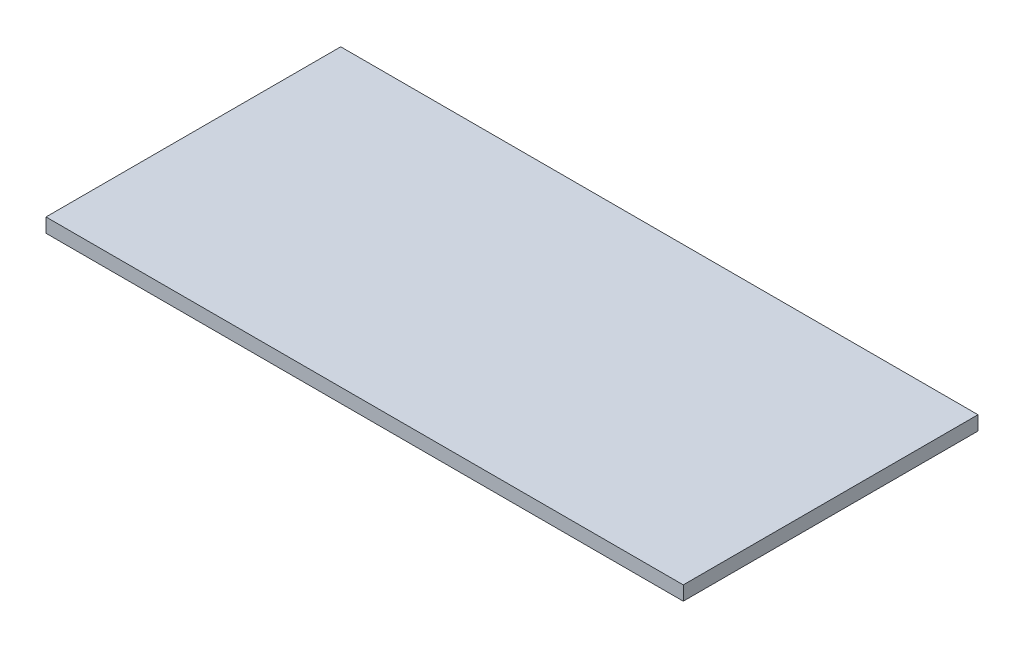
SolidWorks part; units mm, degrees
material "Plywood"
ref_plane "Front Plane" through (0, 0, 0) normal (0, 0, 1) x (1, 0, 0)
ref_plane "Top Plane" through (0, 0, 0) normal (0, 1, 0) x (1, 0, 0)
ref_plane "Right Plane" through (0, 0, 0) normal (1, 0, 0) x (0, 0, -1)
sketch "Sketch2" plane through (0, 0, 0) normal (0, 1, 0) x (1, 0, 0)
  line L1 (0, 0) -> (1143, 0)
  line L2 (0, 0) -> (0, 528.6375)
  line L3 (0, 528.6375) -> (1143, 528.6375)
  line L4 (1143, 0) -> (1143, 528.6375)
  dimension "D1" = 1143
  dimension "D2" = 528.6375
extrude "Boss-Extrude1" add sketch "Sketch2" along normal blind 25.4
